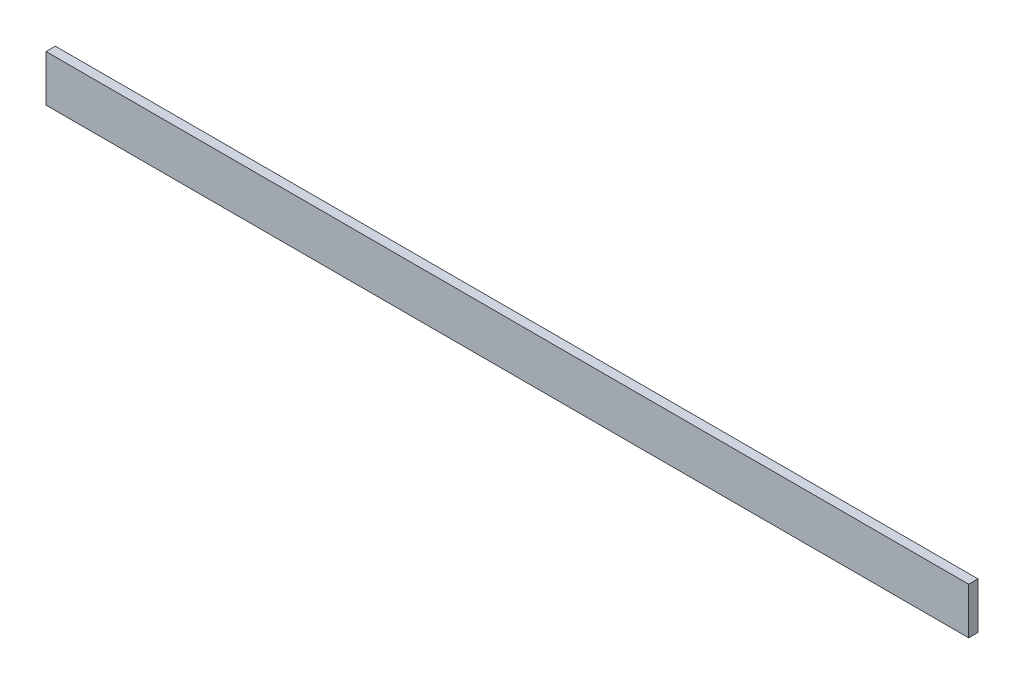
SolidWorks part; units mm, degrees
material "Elastomère naturel (NR)"
ref_plane "Plan de face" through (0, 0, 0) normal (0, 0, 1) x (1, 0, 0)
ref_plane "Plan de dessus" through (0, 0, 0) normal (0, 1, 0) x (1, 0, 0)
ref_plane "Plan de droite" through (0, 0, 0) normal (1, 0, 0) x (0, 0, -1)
sketch "Esquisse1" plane through (0, 0, 0) normal (0, 0, 1) x (1, 0, 0)
  line L0 (-149, 0) -> (149, 0) construction
  line L1 (-149, 7.5) -> (149, 7.5)
  line L2 (-149, 7.5) -> (-149, -7.5)
  line L3 (-149, -7.5) -> (149, -7.5)
  line L4 (149, 7.5) -> (149, -7.5)
  dimension "D1" = 15
  dimension "D2" = 298
extrude "Extrusion1" add sketch "Esquisse1" along normal mid plane 3
